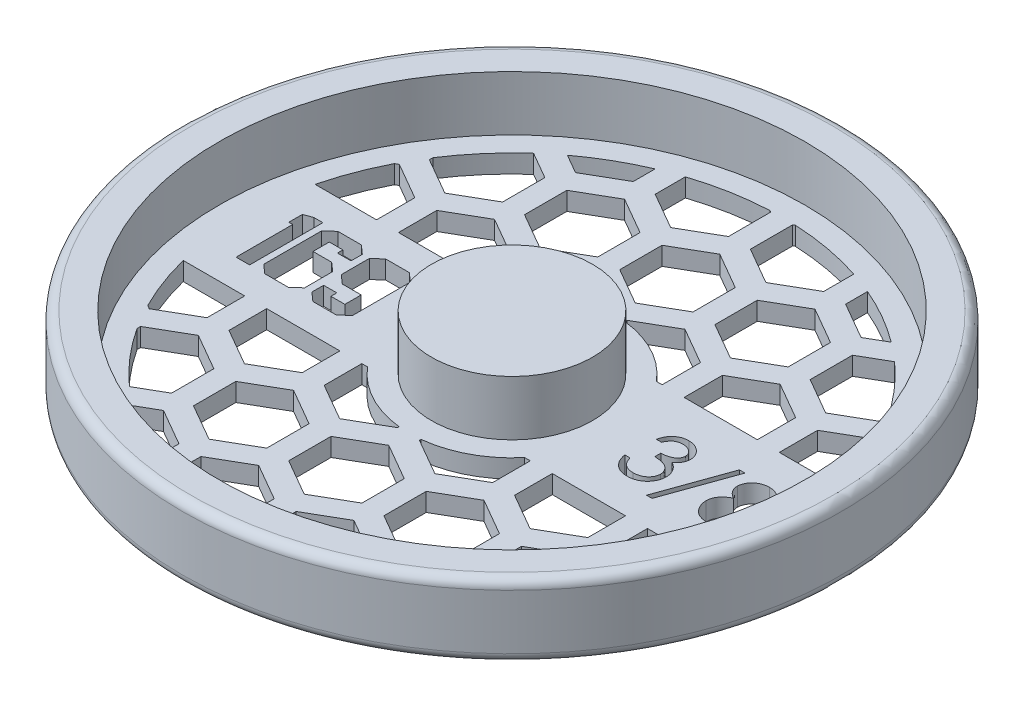
SolidWorks part; units mm, degrees
ref_plane "Front Plane" through (0, 0, 0) normal (0, 0, 1) x (1, 0, 0)
ref_plane "Top Plane" through (0, 0, 0) normal (0, 1, 0) x (1, 0, 0)
ref_plane "Right Plane" through (0, 0, 0) normal (1, 0, 0) x (0, 0, -1)
sketch "Sketch1" plane through (0, 0, 0) normal (0, 0, 1) x (1, 0, 0)
  line L0 (0, 0) -> (0, 12.7)
  line L1 (0, 12.7) -> (13.97, 12.7)
  line L2 (13.97, 12.7) -> (13.97, 3.175)
  line L3 (13.97, 3.175) -> (50.8, 3.175)
  line L4 (50.8, 3.175) -> (50.8, 12.7)
  line L5 (50.8, 12.7) -> (55.5625, 12.7)
  line L6 (57.15, 11.1125) -> (57.15, 1.5875)
  line L7 (55.5625, 0) -> (0, 0)
  arc A0 (55.5625, 0) -> (57.15, 1.5875) centre (55.5625, 1.5875) ccw
  arc A1 (57.15, 11.1125) -> (55.5625, 12.7) centre (55.5625, 11.1125) ccw
  dimension "D7" = 1.5875
  dimension "D1" = 50.8
  dimension "D2" = 3.175
  dimension "D3" = 6.35
  dimension "D4" = 13.97
  dimension "D5" = 9.525
  dimension "D6" = 9.525
revolve "Revolve1" add sketch "Sketch1" angle 360 about L0
sketch "Sketch3" plane through (0, 3.175, 0) normal (0, 1, 0) x (1, 0, 0)
  line L0 (-13.97, 0) -> (-50.8, 0) construction
  line L1 (-13.97, -6.35) -> (-50.8, -6.35) construction
  line L2 (13.97, 0) -> (50.8, 0) construction
  line L3 (13.97, -5.08) -> (50.8, -5.08) construction
  circle A0 centre (0, 0) radius 13.97 construction
  circle A1 centre (0, 0) radius 13.97 construction
  circle A2 centre (0, 0) radius 50.8 construction
  circle A3 centre (0, 0) radius 50.8 construction
  text T0 "169" font "Jersey M54" height 12.7
  text T1 "3/8" font "Century Gothic" height 10.16
  dimension "D1" = 6.35
  dimension "D2" = 5.08
extrude "Cut-Extrude2" cut sketch "Sketch3" against normal through all both and the other way through all
sketch "Sketch4" plane through (0, 3.175, 0) normal (0, 1, 0) x (1, 0, 0)
  line L0 (10.16, -3.6662) -> (16.51, -7.3323)
  line L1 (0, -7.3323) -> (6.35, -3.6662)
  line L2 (6.35, -3.6662) -> (6.35, 3.6662)
  line L3 (6.35, 3.6662) -> (0, 7.3323)
  line L4 (0, 7.3323) -> (-6.35, 3.6662)
  line L5 (-6.35, 3.6662) -> (-6.35, -3.6662)
  line L6 (-6.35, -3.6662) -> (0, -7.3323)
  line L7 (8.255, -21.6304) -> (14.605, -17.9643)
  line L8 (14.605, -17.9643) -> (14.605, -10.6319)
  line L9 (14.605, -10.6319) -> (8.255, -6.9657)
  line L10 (8.255, -6.9657) -> (1.905, -10.6319)
  line L11 (1.905, -10.6319) -> (1.905, -17.9643)
  line L12 (1.905, -17.9643) -> (8.255, -21.6304)
  line L13 (10.16, 3.6662) -> (10.16, -3.6662)
  line L14 (16.51, 7.3323) -> (10.16, 3.6662)
  line L15 (22.86, 3.6662) -> (16.51, 7.3323)
  line L16 (22.86, -3.6662) -> (22.86, 3.6662)
  line L17 (16.51, -7.3323) -> (22.86, -3.6662)
  line L18 (24.765, -21.6304) -> (31.115, -17.9643)
  line L19 (31.115, -17.9643) -> (31.115, -10.6319)
  line L20 (31.115, -10.6319) -> (24.765, -6.9657)
  line L21 (24.765, -6.9657) -> (18.415, -10.6319)
  line L22 (18.415, -10.6319) -> (18.415, -17.9643)
  line L23 (18.415, -17.9643) -> (24.765, -21.6304)
  line L24 (26.67, -3.6662) -> (33.02, -7.3323)
  line L25 (26.67, 3.6662) -> (26.67, -3.6662)
  line L26 (33.02, 7.3323) -> (26.67, 3.6662)
  line L27 (39.37, 3.6662) -> (33.02, 7.3323)
  line L28 (39.37, -3.6662) -> (39.37, 3.6662)
  line L29 (33.02, -7.3323) -> (39.37, -3.6662)
  line L30 (41.275, -21.6304) -> (47.625, -17.9643)
  line L31 (47.625, -17.9643) -> (47.625, -10.6319)
  line L32 (47.625, -10.6319) -> (41.275, -6.9657)
  line L33 (41.275, -6.9657) -> (34.925, -10.6319)
  line L34 (34.925, -10.6319) -> (34.925, -17.9643)
  line L35 (34.925, -17.9643) -> (41.275, -21.6304)
  line L36 (43.18, -3.6662) -> (49.53, -7.3323)
  line L37 (43.18, 3.6662) -> (43.18, -3.6662)
  line L38 (49.53, 7.3323) -> (43.18, 3.6662)
  line L39 (55.88, 3.6662) -> (49.53, 7.3323)
  line L40 (55.88, -3.6662) -> (55.88, 3.6662)
  line L41 (49.53, -7.3323) -> (55.88, -3.6662)
  line L42 (57.785, -21.6304) -> (64.135, -17.9643)
  line L43 (64.135, -17.9643) -> (64.135, -10.6319)
  line L44 (64.135, -10.6319) -> (57.785, -6.9657)
  line L45 (57.785, -6.9657) -> (51.435, -10.6319)
  line L46 (51.435, -10.6319) -> (51.435, -17.9643)
  line L47 (51.435, -17.9643) -> (57.785, -21.6304)
  line L48 (-22.86, -3.6662) -> (-16.51, -7.3323)
  line L49 (-22.86, 3.6662) -> (-22.86, -3.6662)
  line L50 (-16.51, 7.3323) -> (-22.86, 3.6662)
  line L51 (-10.16, 3.6662) -> (-16.51, 7.3323)
  line L52 (-10.16, -3.6662) -> (-10.16, 3.6662)
  line L53 (-16.51, -7.3323) -> (-10.16, -3.6662)
  line L54 (-8.255, -21.6304) -> (-1.905, -17.9643)
  line L55 (-1.905, -17.9643) -> (-1.905, -10.6319)
  line L56 (-1.905, -10.6319) -> (-8.255, -6.9657)
  line L57 (-8.255, -6.9657) -> (-14.605, -10.6319)
  line L58 (-14.605, -10.6319) -> (-14.605, -17.9643)
  line L59 (-14.605, -17.9643) -> (-8.255, -21.6304)
  line L60 (-39.37, -3.6662) -> (-33.02, -7.3323)
  line L61 (-39.37, 3.6662) -> (-39.37, -3.6662)
  line L62 (-33.02, 7.3323) -> (-39.37, 3.6662)
  line L63 (-26.67, 3.6662) -> (-33.02, 7.3323)
  line L64 (-26.67, -3.6662) -> (-26.67, 3.6662)
  line L65 (-33.02, -7.3323) -> (-26.67, -3.6662)
  line L66 (-24.765, -21.6304) -> (-18.415, -17.9643)
  line L67 (-18.415, -17.9643) -> (-18.415, -10.6319)
  line L68 (-18.415, -10.6319) -> (-24.765, -6.9657)
  line L69 (-24.765, -6.9657) -> (-31.115, -10.6319)
  line L70 (-31.115, -10.6319) -> (-31.115, -17.9643)
  line L71 (-31.115, -17.9643) -> (-24.765, -21.6304)
  line L72 (-55.88, -3.6662) -> (-49.53, -7.3323)
  line L73 (-55.88, 3.6662) -> (-55.88, -3.6662)
  line L74 (-49.53, 7.3323) -> (-55.88, 3.6662)
  line L75 (-43.18, 3.6662) -> (-49.53, 7.3323)
  line L76 (-43.18, -3.6662) -> (-43.18, 3.6662)
  line L77 (-49.53, -7.3323) -> (-43.18, -3.6662)
  line L78 (-41.275, -21.6304) -> (-34.925, -17.9643)
  line L79 (-34.925, -17.9643) -> (-34.925, -10.6319)
  line L80 (-34.925, -10.6319) -> (-41.275, -6.9657)
  line L81 (-41.275, -6.9657) -> (-47.625, -10.6319)
  line L82 (-47.625, -10.6319) -> (-47.625, -17.9643)
  line L83 (-47.625, -17.9643) -> (-41.275, -21.6304)
  line L84 (-6.35, 25.0358) -> (0, 21.3697)
  line L85 (-6.35, 32.3682) -> (-6.35, 25.0358)
  line L86 (0, 36.0343) -> (-6.35, 32.3682)
  line L87 (6.35, 32.3682) -> (0, 36.0343)
  line L88 (6.35, 25.0358) -> (6.35, 32.3682)
  line L89 (0, 21.3697) -> (6.35, 25.0358)
  line L90 (8.255, 7.0716) -> (14.605, 10.7377)
  line L91 (14.605, 10.7377) -> (14.605, 18.0701)
  line L92 (14.605, 18.0701) -> (8.255, 21.7363)
  line L93 (8.255, 21.7363) -> (1.905, 18.0701)
  line L94 (1.905, 18.0701) -> (1.905, 10.7377)
  line L95 (1.905, 10.7377) -> (8.255, 7.0716)
  line L96 (-8.255, 7.0716) -> (-1.905, 10.7377)
  line L97 (-1.905, 10.7377) -> (-1.905, 18.0701)
  line L98 (-1.905, 18.0701) -> (-8.255, 21.7363)
  line L99 (-8.255, 21.7363) -> (-14.605, 18.0701)
  line L100 (-14.605, 18.0701) -> (-14.605, 10.7377)
  line L101 (-14.605, 10.7377) -> (-8.255, 7.0716)
  line L102 (-22.86, 25.0358) -> (-16.51, 21.3697)
  line L103 (-16.51, 21.3697) -> (-10.16, 25.0358)
  line L104 (-10.16, 25.0358) -> (-10.16, 32.3682)
  line L105 (-10.16, 32.3682) -> (-16.51, 36.0343)
  line L106 (-16.51, 36.0343) -> (-22.86, 32.3682)
  line L107 (-22.86, 32.3682) -> (-22.86, 25.0358)
  line L108 (-24.765, 7.0716) -> (-18.415, 10.7377)
  line L109 (-18.415, 10.7377) -> (-18.415, 18.0701)
  line L110 (-18.415, 18.0701) -> (-24.765, 21.7363)
  line L111 (-24.765, 21.7363) -> (-31.115, 18.0701)
  line L112 (-31.115, 18.0701) -> (-31.115, 10.7377)
  line L113 (-31.115, 10.7377) -> (-24.765, 7.0716)
  line L114 (-39.37, 25.0358) -> (-33.02, 21.3697)
  line L115 (-33.02, 21.3697) -> (-26.67, 25.0358)
  line L116 (-26.67, 25.0358) -> (-26.67, 32.3682)
  line L117 (-26.67, 32.3682) -> (-33.02, 36.0343)
  line L118 (-33.02, 36.0343) -> (-39.37, 32.3682)
  line L119 (-39.37, 32.3682) -> (-39.37, 25.0358)
  line L120 (-55.88, 25.0358) -> (-49.53, 21.3697)
  line L121 (-49.53, 21.3697) -> (-43.18, 25.0358)
  line L122 (-43.18, 25.0358) -> (-43.18, 32.3682)
  line L123 (-43.18, 32.3682) -> (-49.53, 36.0343)
  line L124 (-49.53, 36.0343) -> (-55.88, 32.3682)
  line L125 (-55.88, 32.3682) -> (-55.88, 25.0358)
  line L126 (-41.275, 7.0716) -> (-34.925, 10.7377)
  line L127 (-34.925, 10.7377) -> (-34.925, 18.0701)
  line L128 (-34.925, 18.0701) -> (-41.275, 21.7363)
  line L129 (-41.275, 21.7363) -> (-47.625, 18.0701)
  line L130 (-47.625, 18.0701) -> (-47.625, 10.7377)
  line L131 (-47.625, 10.7377) -> (-41.275, 7.0716)
  line L132 (10.16, 25.0358) -> (16.51, 21.3697)
  line L133 (16.51, 21.3697) -> (22.86, 25.0358)
  line L134 (22.86, 25.0358) -> (22.86, 32.3682)
  line L135 (22.86, 32.3682) -> (16.51, 36.0343)
  line L136 (16.51, 36.0343) -> (10.16, 32.3682)
  line L137 (10.16, 32.3682) -> (10.16, 25.0358)
  line L138 (24.765, 7.0716) -> (31.115, 10.7377)
  line L139 (31.115, 10.7377) -> (31.115, 18.0701)
  line L140 (31.115, 18.0701) -> (24.765, 21.7363)
  line L141 (24.765, 21.7363) -> (18.415, 18.0701)
  line L142 (18.415, 18.0701) -> (18.415, 10.7377)
  line L143 (18.415, 10.7377) -> (24.765, 7.0716)
  line L144 (26.67, 25.0358) -> (33.02, 21.3697)
  line L145 (33.02, 21.3697) -> (39.37, 25.0358)
  line L146 (39.37, 25.0358) -> (39.37, 32.3682)
  line L147 (39.37, 32.3682) -> (33.02, 36.0343)
  line L148 (33.02, 36.0343) -> (26.67, 32.3682)
  line L149 (26.67, 32.3682) -> (26.67, 25.0358)
  line L150 (41.275, 7.0716) -> (47.625, 10.7377)
  line L151 (47.625, 10.7377) -> (47.625, 18.0701)
  line L152 (47.625, 18.0701) -> (41.275, 21.7363)
  line L153 (41.275, 21.7363) -> (34.925, 18.0701)
  line L154 (34.925, 18.0701) -> (34.925, 10.7377)
  line L155 (34.925, 10.7377) -> (41.275, 7.0716)
  line L156 (43.18, 25.0358) -> (49.53, 21.3697)
  line L157 (49.53, 21.3697) -> (55.88, 25.0358)
  line L158 (55.88, 25.0358) -> (55.88, 32.3682)
  line L159 (55.88, 32.3682) -> (49.53, 36.0343)
  line L160 (49.53, 36.0343) -> (43.18, 32.3682)
  line L161 (43.18, 32.3682) -> (43.18, 25.0358)
  line L162 (57.785, 7.0716) -> (64.135, 10.7377)
  line L163 (64.135, 10.7377) -> (64.135, 18.0701)
  line L164 (64.135, 18.0701) -> (57.785, 21.7363)
  line L165 (57.785, 21.7363) -> (51.435, 18.0701)
  line L166 (51.435, 18.0701) -> (51.435, 10.7377)
  line L167 (51.435, 10.7377) -> (57.785, 7.0716)
  line L168 (-6.35, 53.7378) -> (0, 50.0717)
  line L169 (-6.35, 61.0702) -> (-6.35, 53.7378)
  line L170 (0, 64.7363) -> (-6.35, 61.0702)
  line L171 (6.35, 61.0702) -> (0, 64.7363)
  line L172 (6.35, 53.7378) -> (6.35, 61.0702)
  line L173 (0, 50.0717) -> (6.35, 53.7378)
  line L174 (8.255, 35.7736) -> (14.605, 39.4397)
  line L175 (14.605, 39.4397) -> (14.605, 46.7721)
  line L176 (14.605, 46.7721) -> (8.255, 50.4383)
  line L177 (8.255, 50.4383) -> (1.905, 46.7721)
  line L178 (1.905, 46.7721) -> (1.905, 39.4397)
  line L179 (1.905, 39.4397) -> (8.255, 35.7736)
  line L180 (-8.255, 35.7736) -> (-1.905, 39.4397)
  line L181 (-1.905, 39.4397) -> (-1.905, 46.7721)
  line L182 (-1.905, 46.7721) -> (-8.255, 50.4383)
  line L183 (-8.255, 50.4383) -> (-14.605, 46.7721)
  line L184 (-14.605, 46.7721) -> (-14.605, 39.4397)
  line L185 (-14.605, 39.4397) -> (-8.255, 35.7736)
  line L186 (-22.86, 53.7378) -> (-16.51, 50.0717)
  line L187 (-16.51, 50.0717) -> (-10.16, 53.7378)
  line L188 (-10.16, 53.7378) -> (-10.16, 61.0702)
  line L189 (-10.16, 61.0702) -> (-16.51, 64.7363)
  line L190 (-16.51, 64.7363) -> (-22.86, 61.0702)
  line L191 (-22.86, 61.0702) -> (-22.86, 53.7378)
  line L192 (-24.765, 35.7736) -> (-18.415, 39.4397)
  line L193 (-18.415, 39.4397) -> (-18.415, 46.7721)
  line L194 (-18.415, 46.7721) -> (-24.765, 50.4383)
  line L195 (-24.765, 50.4383) -> (-31.115, 46.7721)
  line L196 (-31.115, 46.7721) -> (-31.115, 39.4397)
  line L197 (-31.115, 39.4397) -> (-24.765, 35.7736)
  line L198 (-39.37, 53.7378) -> (-33.02, 50.0717)
  line L199 (-33.02, 50.0717) -> (-26.67, 53.7378)
  line L200 (-26.67, 53.7378) -> (-26.67, 61.0702)
  line L201 (-26.67, 61.0702) -> (-33.02, 64.7363)
  line L202 (-33.02, 64.7363) -> (-39.37, 61.0702)
  line L203 (-39.37, 61.0702) -> (-39.37, 53.7378)
  line L204 (-55.88, 53.7378) -> (-49.53, 50.0717)
  line L205 (-49.53, 50.0717) -> (-43.18, 53.7378)
  line L206 (-43.18, 53.7378) -> (-43.18, 61.0702)
  line L207 (-43.18, 61.0702) -> (-49.53, 64.7363)
  line L208 (-49.53, 64.7363) -> (-55.88, 61.0702)
  line L209 (-55.88, 61.0702) -> (-55.88, 53.7378)
  line L210 (-41.275, 35.7736) -> (-34.925, 39.4397)
  line L211 (-34.925, 39.4397) -> (-34.925, 46.7721)
  line L212 (-34.925, 46.7721) -> (-41.275, 50.4383)
  line L213 (-41.275, 50.4383) -> (-47.625, 46.7721)
  line L214 (-47.625, 46.7721) -> (-47.625, 39.4397)
  line L215 (-47.625, 39.4397) -> (-41.275, 35.7736)
  line L216 (10.16, 53.7378) -> (16.51, 50.0717)
  line L217 (16.51, 50.0717) -> (22.86, 53.7378)
  line L218 (22.86, 53.7378) -> (22.86, 61.0702)
  line L219 (22.86, 61.0702) -> (16.51, 64.7363)
  line L220 (16.51, 64.7363) -> (10.16, 61.0702)
  line L221 (10.16, 61.0702) -> (10.16, 53.7378)
  line L222 (24.765, 35.7736) -> (31.115, 39.4397)
  line L223 (31.115, 39.4397) -> (31.115, 46.7721)
  line L224 (31.115, 46.7721) -> (24.765, 50.4383)
  line L225 (24.765, 50.4383) -> (18.415, 46.7721)
  line L226 (18.415, 46.7721) -> (18.415, 39.4397)
  line L227 (18.415, 39.4397) -> (24.765, 35.7736)
  line L228 (26.67, 53.7378) -> (33.02, 50.0717)
  line L229 (33.02, 50.0717) -> (39.37, 53.7378)
  line L230 (39.37, 53.7378) -> (39.37, 61.0702)
  line L231 (39.37, 61.0702) -> (33.02, 64.7363)
  line L232 (33.02, 64.7363) -> (26.67, 61.0702)
  line L233 (26.67, 61.0702) -> (26.67, 53.7378)
  line L234 (41.275, 35.7736) -> (47.625, 39.4397)
  line L235 (47.625, 39.4397) -> (47.625, 46.7721)
  line L236 (47.625, 46.7721) -> (41.275, 50.4383)
  line L237 (41.275, 50.4383) -> (34.925, 46.7721)
  line L238 (34.925, 46.7721) -> (34.925, 39.4397)
  line L239 (34.925, 39.4397) -> (41.275, 35.7736)
  line L240 (43.18, 53.7378) -> (49.53, 50.0717)
  line L241 (49.53, 50.0717) -> (55.88, 53.7378)
  line L242 (55.88, 53.7378) -> (55.88, 61.0702)
  line L243 (55.88, 61.0702) -> (49.53, 64.7363)
  line L244 (49.53, 64.7363) -> (43.18, 61.0702)
  line L245 (43.18, 61.0702) -> (43.18, 53.7378)
  line L246 (57.785, 35.7736) -> (64.135, 39.4397)
  line L247 (64.135, 39.4397) -> (64.135, 46.7721)
  line L248 (64.135, 46.7721) -> (57.785, 50.4383)
  line L249 (57.785, 50.4383) -> (51.435, 46.7721)
  line L250 (51.435, 46.7721) -> (51.435, 39.4397)
  line L251 (51.435, 39.4397) -> (57.785, 35.7736)
  line L252 (-6.35, -32.3682) -> (0, -36.0343)
  line L253 (-6.35, -25.0358) -> (-6.35, -32.3682)
  line L254 (0, -21.3697) -> (-6.35, -25.0358)
  line L255 (6.35, -25.0358) -> (0, -21.3697)
  line L256 (6.35, -32.3682) -> (6.35, -25.0358)
  line L257 (0, -36.0343) -> (6.35, -32.3682)
  line L258 (8.255, -50.3324) -> (14.605, -46.6663)
  line L259 (14.605, -46.6663) -> (14.605, -39.3339)
  line L260 (14.605, -39.3339) -> (8.255, -35.6677)
  line L261 (8.255, -35.6677) -> (1.905, -39.3339)
  line L262 (1.905, -39.3339) -> (1.905, -46.6663)
  line L263 (1.905, -46.6663) -> (8.255, -50.3324)
  line L264 (-8.255, -50.3324) -> (-1.905, -46.6663)
  line L265 (-1.905, -46.6663) -> (-1.905, -39.3339)
  line L266 (-1.905, -39.3339) -> (-8.255, -35.6677)
  line L267 (-8.255, -35.6677) -> (-14.605, -39.3339)
  line L268 (-14.605, -39.3339) -> (-14.605, -46.6663)
  line L269 (-14.605, -46.6663) -> (-8.255, -50.3324)
  line L270 (-22.86, -32.3682) -> (-16.51, -36.0343)
  line L271 (-16.51, -36.0343) -> (-10.16, -32.3682)
  line L272 (-10.16, -32.3682) -> (-10.16, -25.0358)
  line L273 (-10.16, -25.0358) -> (-16.51, -21.3697)
  line L274 (-16.51, -21.3697) -> (-22.86, -25.0358)
  line L275 (-22.86, -25.0358) -> (-22.86, -32.3682)
  line L276 (-24.765, -50.3324) -> (-18.415, -46.6663)
  line L277 (-18.415, -46.6663) -> (-18.415, -39.3339)
  line L278 (-18.415, -39.3339) -> (-24.765, -35.6677)
  line L279 (-24.765, -35.6677) -> (-31.115, -39.3339)
  line L280 (-31.115, -39.3339) -> (-31.115, -46.6663)
  line L281 (-31.115, -46.6663) -> (-24.765, -50.3324)
  line L282 (-39.37, -32.3682) -> (-33.02, -36.0343)
  line L283 (-33.02, -36.0343) -> (-26.67, -32.3682)
  line L284 (-26.67, -32.3682) -> (-26.67, -25.0358)
  line L285 (-26.67, -25.0358) -> (-33.02, -21.3697)
  line L286 (-33.02, -21.3697) -> (-39.37, -25.0358)
  line L287 (-39.37, -25.0358) -> (-39.37, -32.3682)
  line L288 (-55.88, -32.3682) -> (-49.53, -36.0343)
  line L289 (-49.53, -36.0343) -> (-43.18, -32.3682)
  line L290 (-43.18, -32.3682) -> (-43.18, -25.0358)
  line L291 (-43.18, -25.0358) -> (-49.53, -21.3697)
  line L292 (-49.53, -21.3697) -> (-55.88, -25.0358)
  line L293 (-55.88, -25.0358) -> (-55.88, -32.3682)
  line L294 (-41.275, -50.3324) -> (-34.925, -46.6663)
  line L295 (-34.925, -46.6663) -> (-34.925, -39.3339)
  line L296 (-34.925, -39.3339) -> (-41.275, -35.6677)
  line L297 (-41.275, -35.6677) -> (-47.625, -39.3339)
  line L298 (-47.625, -39.3339) -> (-47.625, -46.6663)
  line L299 (-47.625, -46.6663) -> (-41.275, -50.3324)
  line L300 (10.16, -32.3682) -> (16.51, -36.0343)
  line L301 (16.51, -36.0343) -> (22.86, -32.3682)
  line L302 (22.86, -32.3682) -> (22.86, -25.0358)
  line L303 (22.86, -25.0358) -> (16.51, -21.3697)
  line L304 (16.51, -21.3697) -> (10.16, -25.0358)
  line L305 (10.16, -25.0358) -> (10.16, -32.3682)
  line L306 (24.765, -50.3324) -> (31.115, -46.6663)
  line L307 (31.115, -46.6663) -> (31.115, -39.3339)
  line L308 (31.115, -39.3339) -> (24.765, -35.6677)
  line L309 (24.765, -35.6677) -> (18.415, -39.3339)
  line L310 (18.415, -39.3339) -> (18.415, -46.6663)
  line L311 (18.415, -46.6663) -> (24.765, -50.3324)
  line L312 (26.67, -32.3682) -> (33.02, -36.0343)
  line L313 (33.02, -36.0343) -> (39.37, -32.3682)
  line L314 (39.37, -32.3682) -> (39.37, -25.0358)
  line L315 (39.37, -25.0358) -> (33.02, -21.3697)
  line L316 (33.02, -21.3697) -> (26.67, -25.0358)
  line L317 (26.67, -25.0358) -> (26.67, -32.3682)
  line L318 (41.275, -50.3324) -> (47.625, -46.6663)
  line L319 (47.625, -46.6663) -> (47.625, -39.3339)
  line L320 (47.625, -39.3339) -> (41.275, -35.6677)
  line L321 (41.275, -35.6677) -> (34.925, -39.3339)
  line L322 (34.925, -39.3339) -> (34.925, -46.6663)
  line L323 (34.925, -46.6663) -> (41.275, -50.3324)
  line L324 (43.18, -32.3682) -> (49.53, -36.0343)
  line L325 (49.53, -36.0343) -> (55.88, -32.3682)
  line L326 (55.88, -32.3682) -> (55.88, -25.0358)
  line L327 (55.88, -25.0358) -> (49.53, -21.3697)
  line L328 (49.53, -21.3697) -> (43.18, -25.0358)
  line L329 (43.18, -25.0358) -> (43.18, -32.3682)
  line L330 (57.785, -50.3324) -> (64.135, -46.6663)
  line L331 (64.135, -46.6663) -> (64.135, -39.3339)
  line L332 (64.135, -39.3339) -> (57.785, -35.6677)
  line L333 (57.785, -35.6677) -> (51.435, -39.3339)
  line L334 (51.435, -39.3339) -> (51.435, -46.6663)
  line L335 (51.435, -46.6663) -> (57.785, -50.3324)
  line L336 (0, -11.43) -> (0, 11.43)
  line L337 (52.0496, 11.43) -> (-52.0496, 11.43)
  line L338 (52.0496, -11.43) -> (-52.0496, -11.43)
  line L339 (-52.0496, 11.43) -> (-52.0496, -11.43)
  line L340 (52.0496, 11.43) -> (52.0496, -11.43)
  circle A0 centre (0, 0) radius 6.35 construction
  circle A1 centre (8.255, -14.2981) radius 6.35 construction
  circle A2 centre (0, 0) radius 46.99
  circle A3 centre (0, 0) radius 17.78
  point P18 (3.175, -5.4993)
  point P345 (0, 0)
  point P348 (0, 11.43)
  point P351 (0, -11.43)
  dimension "D10" = 93.98
  dimension "D11" = 35.56
  dimension "D1" = 12.7
  dimension "D2" = 12.7
  dimension "D3" = 3.81
  dimension "D4" = 1.905
  dimension "D9" = 22.86
  dimension "D5" = 4
  dimension "D6" = 4
  dimension "D7" = 3
  dimension "D8" = 2
extrude "Cut-Extrude4" cut sketch "Sketch4" against normal through all both and the other way through all contours L129 A2 L337 L127 L128 | L337 L109 L110 L111 L112 | L117 A2 L119 L114 L115 L116 | L193 A2 L197 L192 | L106 L107 L102 L103 L104 L105 | L182 A2 L184 L185 L180 L181 | L84 L89 L88 L87 L86 L85 | A3 L97 L98 L99 L100 L337 | A3 L337 L91 L92 L93 L94 | L175 A2 L177 L178 L179 L174 | L136 L137 L132 L133 L134 L135 | L222 A2 L226 L227 | L146 A2 L148 L149 L144 L145 | L337 L139 L140 L141 L142 | L337 A2 L152 L153 L154 | L30 A2 L338 L34 L35 | L19 L338 L22 L23 L18 | A3 L11 L12 L7 L8 L338 | L312 A2 L314 L315 L316 L317 | L310 A2 L308 L309 | L304 L305 L300 L301 L302 L303 | L263 A2 L259 L260 L261 L262 | L252 L257 L256 L255 L254 L253 | L268 A2 L264 L265 L266 L267 | L274 L275 L270 L271 L272 L273 | L279 A2 L277 L278 | L287 A2 L283 L284 L285 L286 | L338 A2 L83 L78 L79 | L67 L338 L70 L71 L66 | A3 L338 L58 L59 L54 L55
